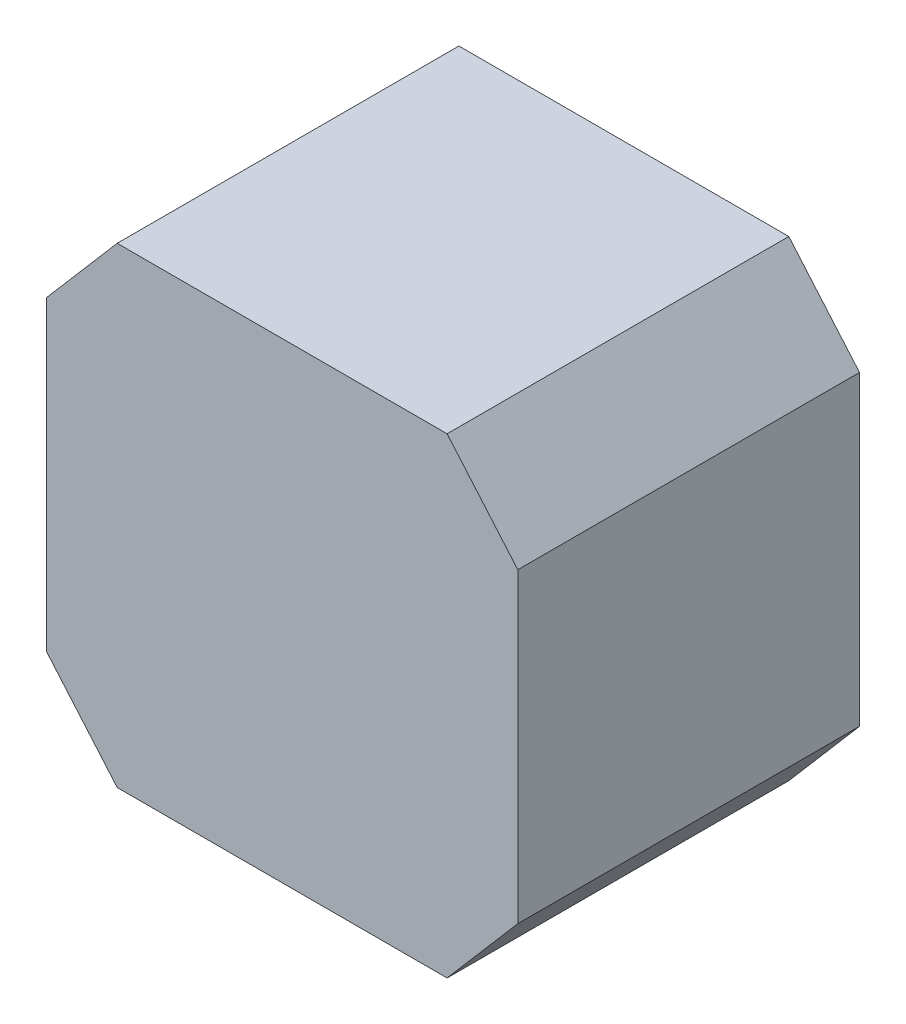
SolidWorks part; units mm, degrees
ref_plane "Alzado" through (0, 0, 0) normal (0, 0, 1) x (1, 0, 0)
ref_plane "Planta" through (0, 0, 0) normal (0, 1, 0) x (1, 0, 0)
ref_plane "Vista lateral" through (0, 0, 0) normal (1, 0, 0) x (0, 0, -1)
sketch "Croquis2" plane through (0, 0, 0) normal (0, 0, 1) x (1, 0, 0)
  line L0 (-20, 8.3463) -> (-14, 8.3463) construction
  line L1 (-14, 20.3226) -> (14, 20.3226)
  line L2 (-20, 13.3275) -> (-20, -12.6824)
  line L3 (-14, -19.6774) -> (14, -19.6774)
  line L4 (20, 13.3275) -> (20, -12.6824)
  line L5 (-20, 20.3226) -> (20, -19.6774) construction
  line L6 (-20, -19.6774) -> (20, 20.3226) construction
  line L7 (-14, 20.3226) -> (-14, 14.3226) construction
  line L8 (-14, 20.3226) -> (-20, 13.3275)
  line L9 (0, 0.3226) -> (0, 5.4483) construction
  line L10 (0, 0.3226) -> (6.8139, 0.3226) construction
  line L11 (14, 20.3226) -> (20, 13.3275)
  line L12 (14, -19.6774) -> (20, -12.6824)
  line L13 (-14, -19.6774) -> (-20, -12.6824)
  point P0 (0, 0.3226)
  dimension "D1" = 40
extrude "Saliente-Extruir1" add sketch "Croquis2" along normal blind 29 contours L1 L11 L4 L12 L3 L13 L2 L8
